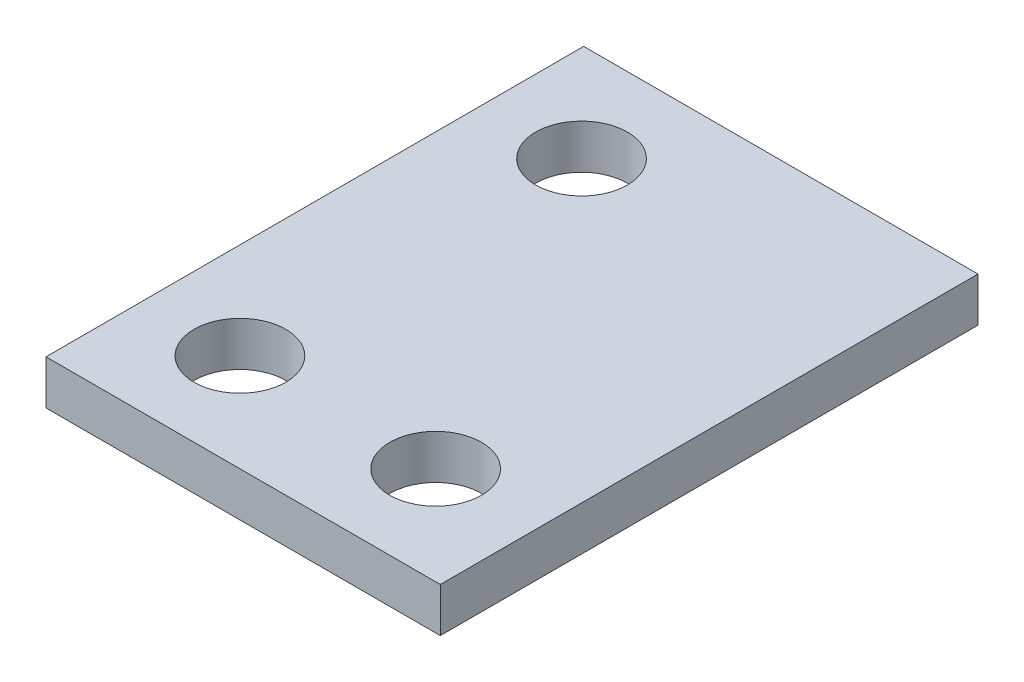
SolidWorks part; units mm, degrees
ref_plane "Front Plane" through (0, 0, 0) normal (0, 0, 1) x (1, 0, 0)
ref_plane "Top Plane" through (0, 0, 0) normal (0, 1, 0) x (1, 0, 0)
ref_plane "Right Plane" through (0, 0, 0) normal (1, 0, 0) x (0, 0, -1)
sketch "Sketch1" plane through (0, 0, 0) normal (0, 1, 0) x (1, 0, 0)
  line L1 (-6.985, 9.525) -> (6.985, 9.525)
  line L2 (-6.985, 9.525) -> (-6.985, -9.525)
  line L3 (-6.985, -9.525) -> (6.985, -9.525)
  line L4 (6.985, 9.525) -> (6.985, -9.525)
  line L5 (-6.985, 9.525) -> (6.985, -9.525) construction
  line L6 (-6.985, -9.525) -> (6.985, 9.525) construction
  point P0 (0, 0)
  dimension "D1" = 13.97
  dimension "D2" = 19.05
extrude "Boss-Extrude1" add sketch "Sketch1" along normal blind 1.57
sketch "Sketch4" plane through (0, 1.57, 0) normal (0, 1, 0) x (1, 0, 0)
  line L0 (-6.985, -7.6835) -> (6.985, -7.6835) construction
  line L1 (-6.985, 9.525) -> (-6.985, -9.525) construction
  line L2 (6.985, -9.525) -> (6.985, 9.525) construction
  line L3 (4.9784, 9.525) -> (4.9784, -9.525) construction
  line L4 (6.985, 9.525) -> (-6.985, 9.525) construction
  line L5 (-6.985, -9.525) -> (6.985, -9.525) construction
  line L6 (-5.207, 9.525) -> (-5.207, -9.525) construction
  line L7 (-6.985, 7.6708) -> (6.985, 7.6708) construction
  circle A0 centre (-3.5814, -6.0579) radius 1.6256
  circle A1 centre (3.3528, -6.0579) radius 1.6256
  circle A2 centre (-3.5814, 6.0452) radius 1.6256
  dimension "D5" = 3.2512
  dimension "D1" = 2.0066
  dimension "D2" = 1.8415
  dimension "D3" = 1.778
  dimension "D4" = 1.8542
extrude "Cut-Extrude1" cut sketch "Sketch4" against normal up to next
